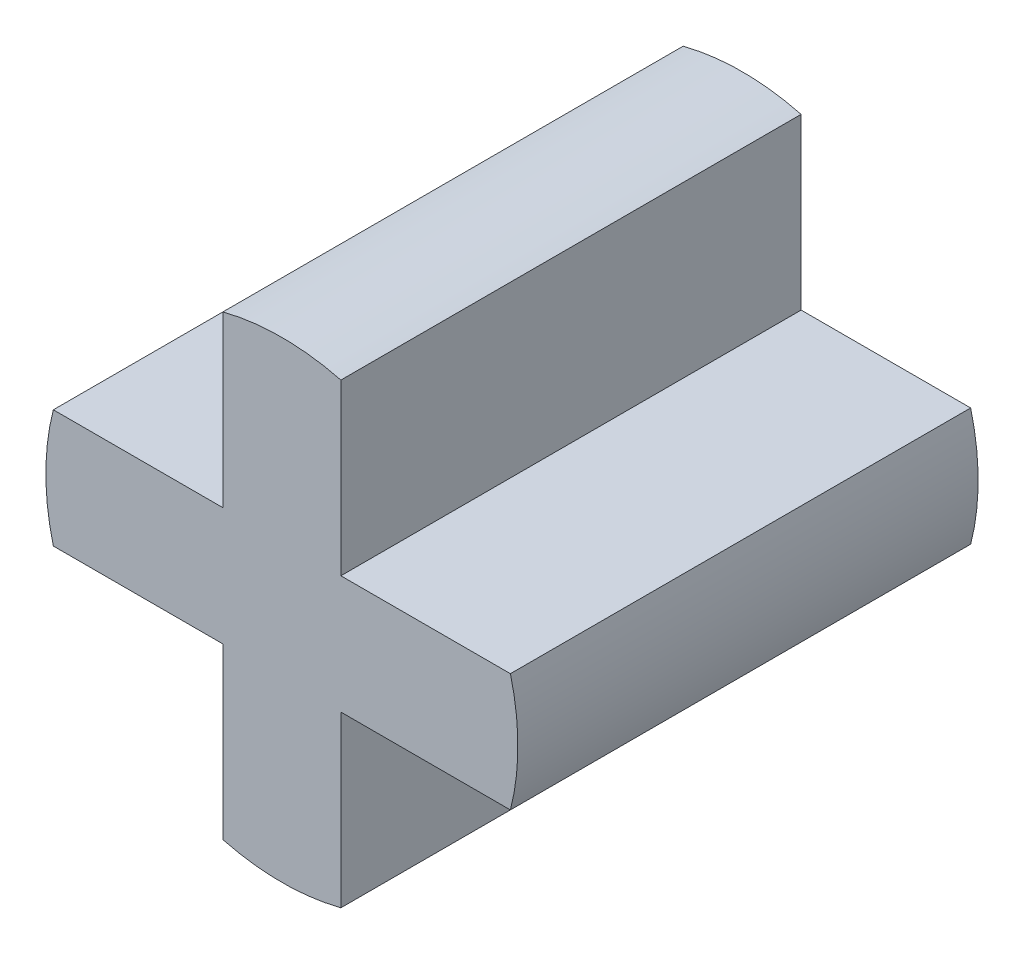
SolidWorks part; units mm, degrees
ref_plane "Front Plane" through (0, 0, 0) normal (0, 0, 1) x (1, 0, 0)
ref_plane "Top Plane" through (0, 0, 0) normal (0, 1, 0) x (1, 0, 0)
ref_plane "Right Plane" through (0, 0, 0) normal (1, 0, 0) x (0, 0, -1)
sketch "Sketch1" plane through (0, 0, 0) normal (0, 0, 1) x (1, 0, 0)
  circle A0 centre (0, 0) radius 4
  dimension "D1" = 8
sketch "Sketch2" plane through (0, 0, 0) normal (0, 0, 1) x (1, 0, 0)
  line L1 (-6.3921, -1) -> (6.3921, -1)
  line L2 (-6.3921, -1) -> (-6.3921, 1)
  line L3 (-6.3921, 1) -> (6.3921, 1)
  line L4 (6.3921, -1) -> (6.3921, 1)
  line L5 (-6.3921, -1) -> (6.3921, 1) construction
  line L6 (-6.3921, 1) -> (6.3921, -1) construction
  line L7 (-1, -6.5242) -> (1, -6.5242)
  line L8 (-1, -6.5242) -> (-1, 6.5242)
  line L9 (-1, 6.5242) -> (1, 6.5242)
  line L10 (1, -6.5242) -> (1, 6.5242)
  line L11 (-1, -6.5242) -> (1, 6.5242) construction
  line L12 (-1, 6.5242) -> (1, -6.5242) construction
  circle A0 centre (0, 0) radius 4 construction
  circle A1 centre (0, 0) radius 4
  dimension "D1" = 2
  dimension "D2" = 2
sketch "Sketch3" plane through (0, 0, 0) normal (0, 0, 1) x (1, 0, 0)
  line L0 (-1, 1) -> (-3.873, 1)
  line L1 (1, -1) -> (3.873, -1)
  line L2 (-1, -1) -> (-1, -3.873)
  line L3 (1, 1) -> (1, 3.873)
  line L4 (-1, -6.5242) -> (1, -6.5242)
  line L5 (1, -6.5242) -> (1, 6.5242)
  line L6 (1, 6.5242) -> (-1, 6.5242)
  line L7 (-1, 6.5242) -> (-1, -6.5242)
  line L9 (1, -3.873) -> (1, -1)
  line L11 (-1, 3.873) -> (-1, 1)
  line L12 (-6.3921, -1) -> (6.3921, -1)
  line L13 (6.3921, -1) -> (6.3921, 1)
  line L14 (6.3921, 1) -> (-6.3921, 1)
  line L15 (-6.3921, 1) -> (-6.3921, -1)
  line L16 (-3.873, -1) -> (-1, -1)
  line L18 (3.873, 1) -> (1, 1)
  arc A0 (-1, -3.873) -> (1, -3.873) centre (0, 0) ccw
  circle A1 centre (0, 0) radius 4
  arc A2 (3.873, -1) -> (3.873, 1) centre (0, 0) ccw
  arc A3 (-3.873, 1) -> (-3.873, -1) centre (0, 0) ccw
  arc A4 (1, 3.873) -> (-1, 3.873) centre (0, 0) ccw
  dimension "D1" = 0
  dimension "D2" = 0
  dimension "D3" = 0
extrude "Boss-Extrude1" add sketch "Sketch3" along normal blind 7.8
